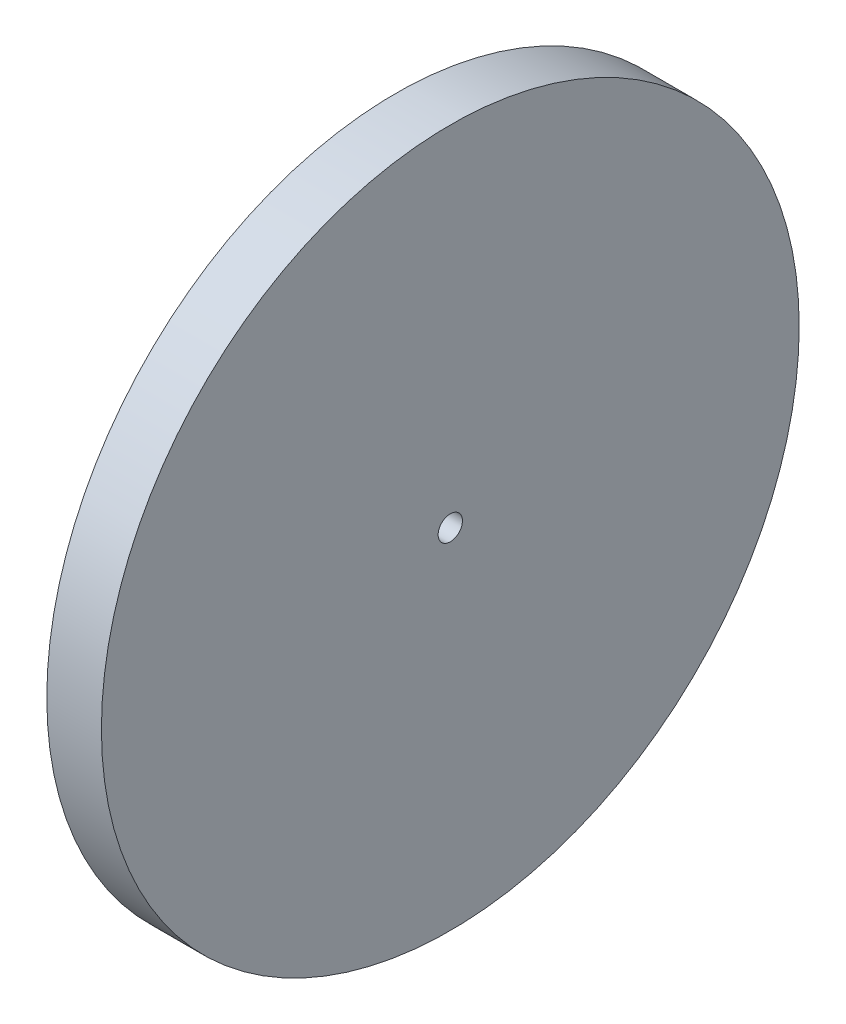
SolidWorks part; units mm, degrees
ref_plane "Plane1" through (0, 0, 0) normal (0, 0, 1) x (1, 0, 0)
ref_plane "Plane2" through (0, 0, 0) normal (0, 1, 0) x (1, 0, 0)
ref_plane "Plane3" through (0, 0, 0) normal (1, 0, 0) x (0, 0, -1)
sketch "HoldingSke" plane through (0, 0, 0) normal (0, 1, 0) x (1, 0, 0)
  line L0 (0, 0) -> (0.3214, -0.383)
  line L1 (-15, 0) -> (100, 0) construction
  line L2 (0, 0) -> (-2.1039, 2.3779)
  line L3 (0, 0) -> (-11.863, 4.5341)
  line L4 (0, 0) -> (5.5511, 6.6156)
  line L5 (0, 0) -> (-23.7986, -8.8762)
  line L6 (0, 0) -> (-10.5278, -7.1032)
  line L7 (-2.1039, 2.3779) -> (3.3635, 27.1825)
  line L8 (-76.2, 4.3779) -> (-54.61, 4.3779)
  line L9 (-71.009, 38.7566) -> (-53.1078, 45.2721)
  line L10 (-76.2, 71.12) -> (104.1128, 71.12)
  line L11 (0, 0) -> (-6, 0)
  line L12 (-76.2, 101.6) -> (-76.133, 101.6)
  line L13 (24.9733, 27.94) -> (52.9518, 28.4284)
  line L14 (24.9733, 27.94) -> (24.9743, 27.94)
  line L15 (24.9733, 27.94) -> (100.4006, 29.5858)
  circle A0 centre (0, 0) radius 57.5
  circle A1 centre (0, 0) radius 12.7
  circle A2 centre (0, 0) radius 12.7
  dimension "MHD" = 25.4
  dimension "Hub_dia" = 25.4
  dimension "Diameter" = 115
  dimension "Num_teeth" = 50
  dimension "Pitch_radius" = 180.3128
  dimension "Pitch" = 0.5
  dimension "Width" = 6
  dimension "Overall_len" = 25.4
  dimension "Show_teeth" = 50
  dimension "Thickness" = 12.7
  dimension "OAL" = 25.4001
  dimension "T_dim" = 21.59
  dimension "Ap" = 20
  dimension "H" = 19.05
  dimension "Backlash" = 0.067
  dimension "Addendum_fac" = 1
  dimension "Dedendum_fac" = 1.25
  dimension "Clearance_fac" = 0.25
  dimension "Dedendum_add" = 0.001
  dimension "Module" = 2
sketch "BasProSke" plane through (0, 0, 0) normal (0, 1, 0) x (1, 0, 0)
  line L0 (-10, 0) -> (60, 0) construction
  line L1 (0, 48) -> (0, 57.5)
  line L2 (0, 48) -> (6, 48)
  line L3 (6, 48) -> (6, 57.5)
  line L4 (6, 57.5) -> (0, 57.5)
  dimension "Diameter" = 115
  dimension "Thickness" = 6
  dimension "Inside_diameter" = 96
revolve "Base-Revolve" add sketch "BasProSke" angle 360 about L0
sketch "TooCutSke" plane through (0, 0, 0) normal (1, 0, 0) x (0, 0, -1)
  line L3 (1.738, 49.9698) -> (1.738, 53.6633) construction
  line L4 (0, 0) -> (0, 59.563) construction
  line L5 (0, 0) -> (-4.2903, 68.1927) construction
  line L6 (-21.6015, 41.0107) -> (35.113, 44.5789) construction
  circle A0 centre (0, 0) radius 50 construction
  circle A1 centre (0, 0) radius 52.501 construction
  circle A2 centre (0, 0) radius 42.2862 construction
  circle A3 centre (0, 0) radius 47.9746 construction
  arc A4 (2.4267, 47.9132) -> (0.6033, 52.4975) centre (-21.6015, 41.0107) ccw
  arc A5 (2.4267, 47.9132) -> (-2.4267, 47.9132) centre (0, 0) ccw
  arc A6 (0.6033, 52.4975) -> (-0.6033, 52.4975) centre (0, 0) ccw
  arc A7 (-0.6033, 52.4975) -> (-2.4267, 47.9132) centre (21.6015, 41.0107) ccw
  dimension "Pitch_dia" = 100
  dimension "Base_dia" = 84.5723
  dimension "Root_dia" = 105.002
  dimension "Overcut_dia" = 95.9492
  dimension "Flank_rad" = 25
  dimension "Half_ang" = 3.6
  dimension "Half_CT" = 1.738
extrude "ToothCut" cut sketch "TooCutSke" along normal through all
fillet "Breaks" [suppressed] radius 0.2
fillet "RootFillets" [suppressed] radius 0.501
pattern_circular "TeethCuts" count 50 over 360 about axis through (0, 0, 0) along (1, 0, 0) of "RootFillets", "Breaks", "ToothCut"
sketch "Esquisse1" plane through (6, 0, 0) normal (1, 0, 0) x (0, 0, -1)
  circle A0 centre (0, 0) radius 57.5
  circle A1 centre (0, 0) radius 2
  dimension "D1" = 115
  dimension "D2" = 4
extrude "Boss.-Extru.1" add sketch "Esquisse1" along normal blind 3
sketch "Esquisse2" plane through (6, 0, 0) normal (-1, 0, 0) x (0, 0, 1)
  circle A0 centre (0, 0) radius 10
  circle A1 centre (0, 0) radius 2
  dimension "D1" = 20
extrude "Boss.-Extru.2" add sketch "Esquisse2" along normal blind 10
sketch "Esquisse3" plane through (-4, 0, 0) normal (-1, 0, 0) x (0, 0, 1)
  line L0 (0, 10) -> (0, -10) construction
  line L1 (-2.75, 6) -> (2.75, 6)
  line L2 (-2.75, 6) -> (-2.75, 4)
  line L3 (-2.75, 4) -> (2.75, 4)
  line L4 (2.75, 6) -> (2.75, 4)
  line L5 (-2.75, 6) -> (2.75, 4) construction
  line L6 (-2.75, 4) -> (2.75, 6) construction
  line L7 (-10, 0) -> (10, 0) construction
  circle A0 centre (0, 0) radius 10 construction
  circle A1 centre (0, 0) radius 10 construction
  point P0 (0, 5)
  dimension "D1" = 5.5
  dimension "D2" = 2
  dimension "D3" = 5
extrude "Enlèv. mat.-Extru.1" cut sketch "Esquisse3" against normal blind 7
sketch "Esquisse4" plane through (0, 4, 0) normal (0, 1, 0) x (1, 0, 0)
  circle A0 centre (0, 0) radius 1.5
  dimension "D1" = 3
extrude "Enlèv. mat.-Extru.2" cut sketch "Esquisse4" against normal up to next and the other way up to next
equation "' \"Module@HoldingSke\" = 6.35"
equation "' \"Num_teeth@HoldingSke\" = 24"
equation "' \"Ap@HoldingSke\" =  14.5"
equation "' \"Width@HoldingSke\" = 12"
equation "' \"Diameter@HoldingSke\" = 8 * 25.4"
equation "' \"Show_teeth@HoldingSke\" = 100"
equation "' \"Backlash@HoldingSke\" = 0.009 * 25.4"
equation "' \"Addendum_fac@HoldingSke\" = 1.0"
equation "' \"Dedendum_fac@HoldingSke\" = 1.25"
equation "' \"Dedendum_add@HoldingSke\" = 0.00005 * 25.4"
equation "' \"Clearance_fac@HoldingSke\" = 0.25"
equation "\"Pitch@HoldingSke\" = 1 / \"Module@HoldingSke\" "
equation "\"Overcut_dia@TooCutSke\" = (\"Num_teeth@HoldingSke\" - 2 * \"Addendum_fac@HoldingSke\") / \"Pitch@HoldingSke\" - 0.002 * 25.4"
equation "\"Pitch_dia@TooCutSke\" = \"Num_teeth@HoldingSke\" / \"Pitch@HoldingSke\""
equation "\"Base_dia@TooCutSke\" = \"Num_teeth@HoldingSke\" / \"Pitch@HoldingSke\" * cos((\"Ap@HoldingSke\"  * 3.14159265 / 180)) * 0.90"
equation "\"Root_dia@TooCutSke\" = \"Num_teeth@HoldingSke\"  / \"Pitch@HoldingSke\" + 2 *  \"Dedendum_fac@HoldingSke\"/ \"Pitch@HoldingSke\" + \"Dedendum_add@HoldingSke\" * 2"
equation "\"Half_ang@TooCutSke\" = 180 / \"Num_teeth@HoldingSke\""
equation "\"Half_CT@TooCutSke\" = \"Num_teeth@HoldingSke\" / \"Pitch@HoldingSke\" * sin((3.14159265 / 2 / \"Num_teeth@HoldingSke\")) / 2 + 10 * \"Backlash@HoldingSke\" / 4"
equation "\"Flank_rad@TooCutSke\" = \"Num_teeth@HoldingSke\" / \"Pitch@HoldingSke\" / 4"
equation "\"Radius@RootFillets\"= \"Clearance_fac@HoldingSke\" / \"Pitch@HoldingSke\" + \"Dedendum_add@HoldingSke\""
equation "\"Break_rad@Breaks\" = 0.02 / \"Pitch@HoldingSke\" * 5"
equation "\"Num_teeth@TeethCuts\" = int( \"Show_teeth@HoldingSke\" ) + 1"
equation "\"Num_teeth@TeethCuts\" = ((sgn( \"Num_teeth@TeethCuts\" - \"Num_teeth@HoldingSke\" )-1)*( \"Num_teeth@TeethCuts\" - \"Num_teeth@HoldingSke\" ))/-2+ \"Num_teeth@HoldingSke\""
equation "\"Num_teeth@TeethCuts\" = ((sgn( \"Num_teeth@TeethCuts\" - 2.0)+1)*( \"Num_teeth@TeethCuts\" - 2.0))/2 +2.0"
equation "\"Angle@TeethCuts\" = 360.0 / \"Num_teeth@HoldingSke\""
equation "\"Diameter@BasProSke\" = \"Num_teeth@HoldingSke\"  / \"Pitch@HoldingSke\" + 2 *  \"Dedendum_fac@HoldingSke\"/ \"Pitch@HoldingSke\" + \"Dedendum_add@HoldingSke\" * 2 + 0.002 * 25.4"
equation "\"Diameter@BasProSke\" = ((sgn( \"Diameter@BasProSke\"  - \"Diameter@HoldingSke\" )+1)*( \"Diameter@BasProSke\"  - \"Diameter@HoldingSke\" ))/2 + \"Diameter@HoldingSke\""
equation "\"Inside_diameter@BasProSke\" =  (\"Num_teeth@HoldingSke\" - 2 * \"Addendum_fac@HoldingSke\") / \"Pitch@HoldingSke\" "
equation "\"Thickness@BasProSke\"  = \"Width@HoldingSke\""
